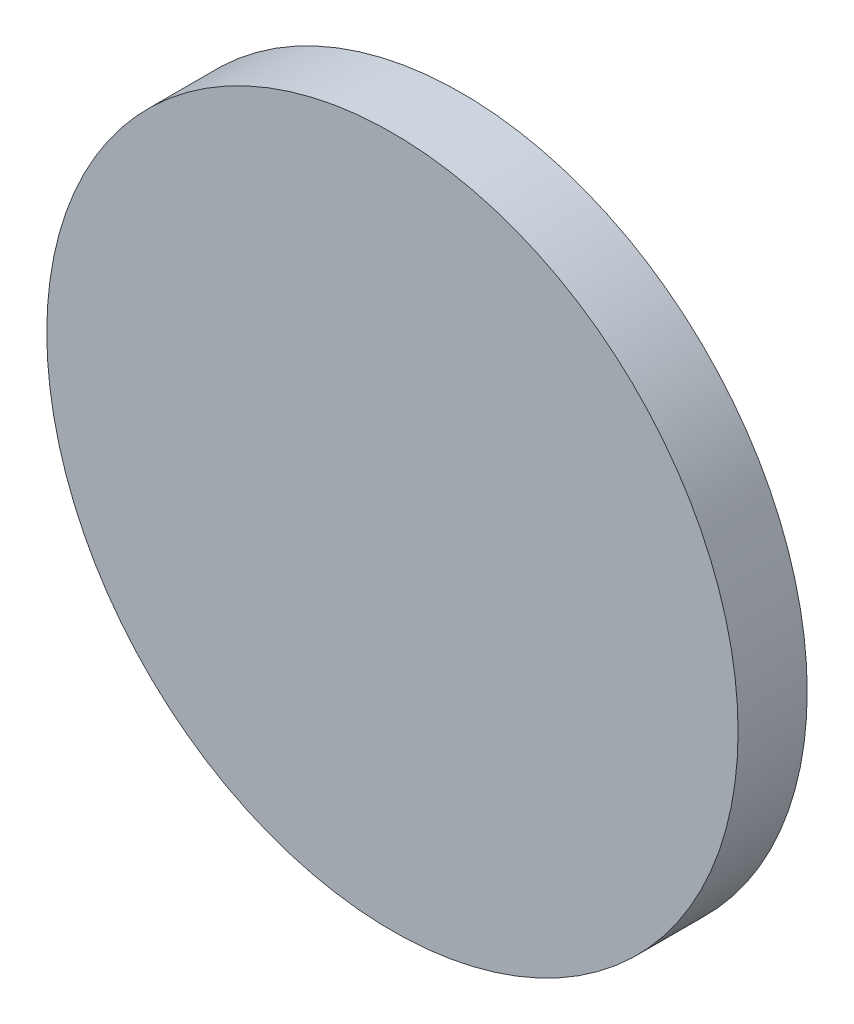
SolidWorks part; units mm, degrees
ref_plane "前视基准面" through (0, 0, 0) normal (0, 0, 1) x (1, 0, 0)
ref_plane "上视基准面" through (0, 0, 0) normal (0, 1, 0) x (1, 0, 0)
ref_plane "右视基准面" through (0, 0, 0) normal (1, 0, 0) x (0, 0, -1)
sketch "草图1" plane through (0, 0, 0) normal (0, 0, 1) x (1, 0, 0)
  circle A0 centre (0, 0) radius 5
  dimension "D1" = 10
extrude "凸台-拉伸1" add sketch "草图1" along normal blind 1 contours A0
